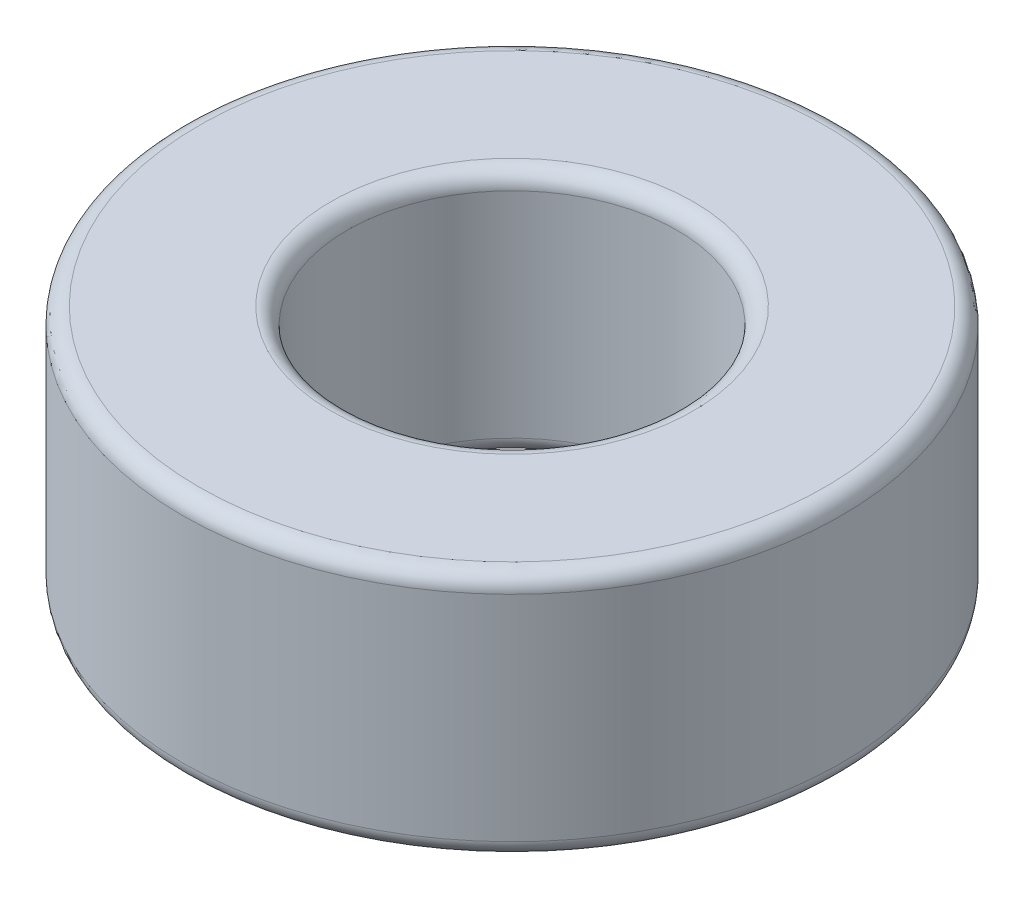
SolidWorks part; units mm, degrees
ref_plane "Front Plane" through (0, 0, 0) normal (0, 0, 1) x (1, 0, 0)
ref_plane "Top Plane" through (0, 0, 0) normal (0, 1, 0) x (1, 0, 0)
ref_plane "Right Plane" through (0, 0, 0) normal (1, 0, 0) x (0, 0, -1)
sketch "Sketch1" plane through (0, 0, 0) normal (0, 1, 0) x (1, 0, 0)
  circle A0 centre (0, 0) radius 10
  circle A1 centre (0, 0) radius 20
  dimension "D1" = 20
  dimension "D2" = 40
extrude "Boss-Extrude2" add sketch "Sketch1" along normal blind 15
fillet "Fillet1" radius 1 1 edges at (0, 15, 20)
fillet "Fillet2" radius 1 1 edges at (0, 15, 10)
fillet "Fillet3" radius 1 2 edges at (0, 0, 10) (0, 0, 20)
